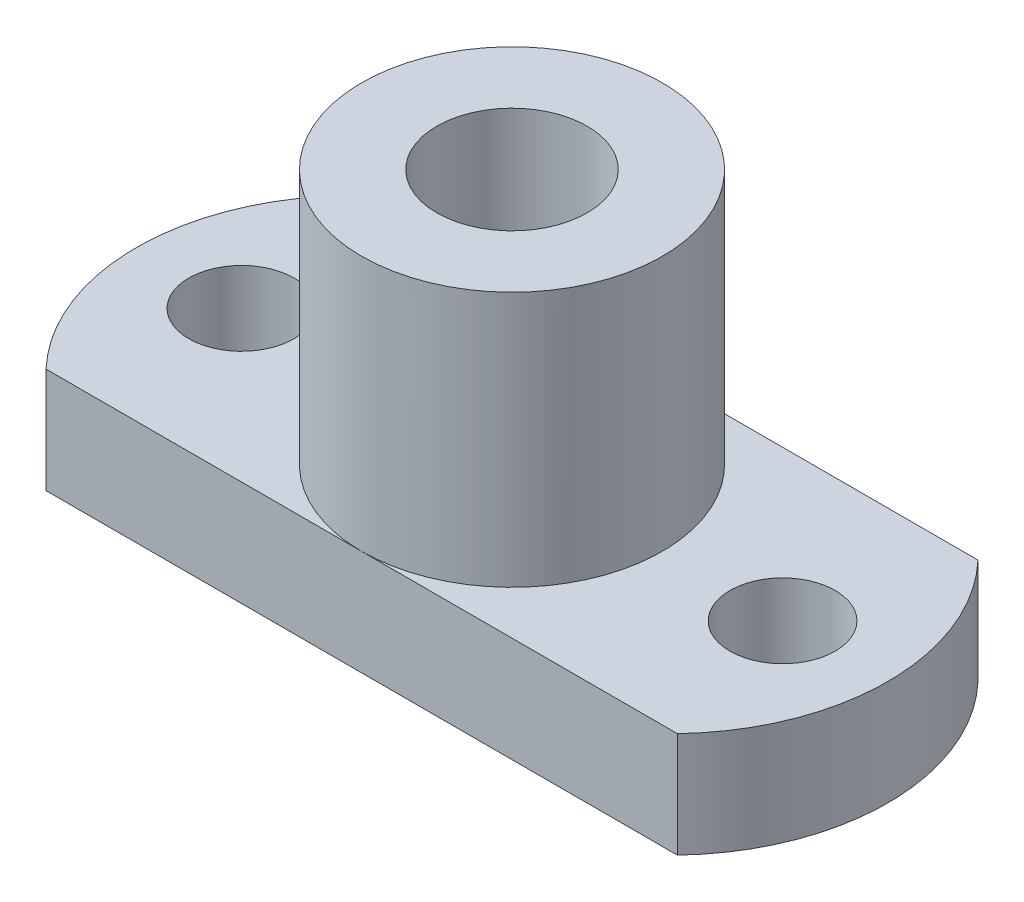
SolidWorks part; units mm, degrees
ref_plane "Front Plane" through (0, 0, 0) normal (0, 0, 1) x (1, 0, 0)
ref_plane "Top Plane" through (0, 0, 0) normal (0, 1, 0) x (1, 0, 0)
ref_plane "Right Plane" through (0, 0, 0) normal (1, 0, 0) x (0, 0, -1)
sketch "Sketch1" plane through (0, 0, 0) normal (0, 1, 0) x (1, 0, 0)
  circle A0 centre (0, 0) radius 5
  circle A1 centre (0, 0) radius 2.5
  dimension "D1" = 5
  dimension "D2" = 10
extrude "Boss-Extrude1" add sketch "Sketch1" along normal blind 12
sketch "Sketch2" plane through (0, 0, 0) normal (0, 1, 0) x (1, 0, 0)
  line L0 (0, -5) -> (-10.5, -5)
  line L1 (0, -5) -> (0, 5) construction
  line L2 (-10.5, 5) -> (0, 5)
  line L3 (-9, 0) -> (0, 0) construction
  line L5 (-10.5, -5) -> (-10.5, 5) construction
  arc A0 (-10.5, -5) -> (-10.5, 5) centre (-5.25, 0) cw
  circle A1 centre (-9, 0) radius 1.75
  circle A2 centre (0, 0) radius 5 construction
  arc A3 (0, 5) -> (0, -5) centre (0, 0) ccw
  point P5 (-12.5, 0)
  dimension "D4" = 3.5
  dimension "D1" = 1.5
  dimension "D2" = 12.5
  dimension "D3" = 9
extrude "Boss-Extrude2" add sketch "Sketch2" along normal blind 3.5
mirror "Mirror1" about plane through (0, 0, 0) normal (1, 0, 0) of "Boss-Extrude2"
